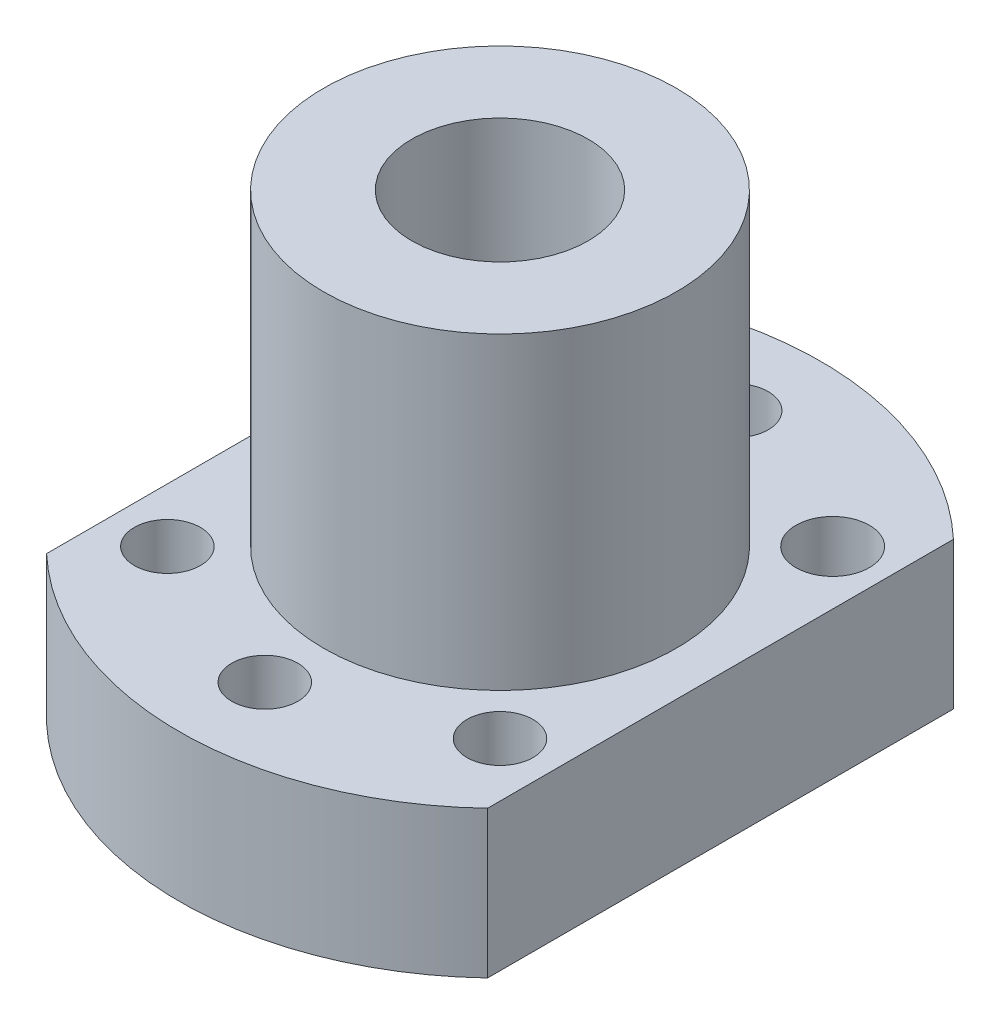
SolidWorks part; units mm, degrees
ref_plane "前视基准面" through (0, 0, 0) normal (0, 0, 1) x (1, 0, 0)
ref_plane "上视基准面" through (0, 0, 0) normal (0, 1, 0) x (1, 0, 0)
ref_plane "右视基准面" through (0, 0, 0) normal (1, 0, 0) x (0, 0, -1)
other "Configuration Table"
sketch "草图1" plane through (0, 0, 0) normal (0, 1, 0) x (1, 0, 0)
  line L0 (-15, 15.8463) -> (-15, -15.8463)
  line L1 (15, 15.8463) -> (15, -15.8463)
  line L2 (-11.3137, 11.3137) -> (0, 0) construction
  line L3 (11.3137, 11.3137) -> (0, 0) construction
  line L4 (0, 16) -> (0, 0) construction
  circle A0 centre (0, 0) radius 21.8198
  circle A1 centre (0, 0) radius 16
  circle A2 centre (-11.3137, 11.3137) radius 2.25
  circle A3 centre (0, 16) radius 2.25
  circle A4 centre (11.3137, 11.3137) radius 2.5
  circle A5 centre (0, -16) radius 2.25
  circle A6 centre (-11.3137, -11.3137) radius 2.25
  circle A7 centre (11.3137, -11.3137) radius 2.25
  circle A8 centre (0, 0) radius 6
  dimension "D1" = 30
  dimension "D2" = 45
  dimension "D3" = 45
extrude "凸台-拉伸1" add sketch "草图1" along normal blind 10 contours A7 A1 L1 A4 A3 A2 L0 A6 A5 A8 | A7 A1 A5 A6 L0 A0 L1 | A4 A1 L1 A0 L0 A2 A3
sketch "草图3" plane through (0, 10, 0) normal (0, 1, 0) x (1, 0, 0)
  circle A0 centre (0, 0) radius 12
  circle A1 centre (0, 0) radius 6
extrude "凸台-拉伸2" add sketch "草图3" along normal blind 21
